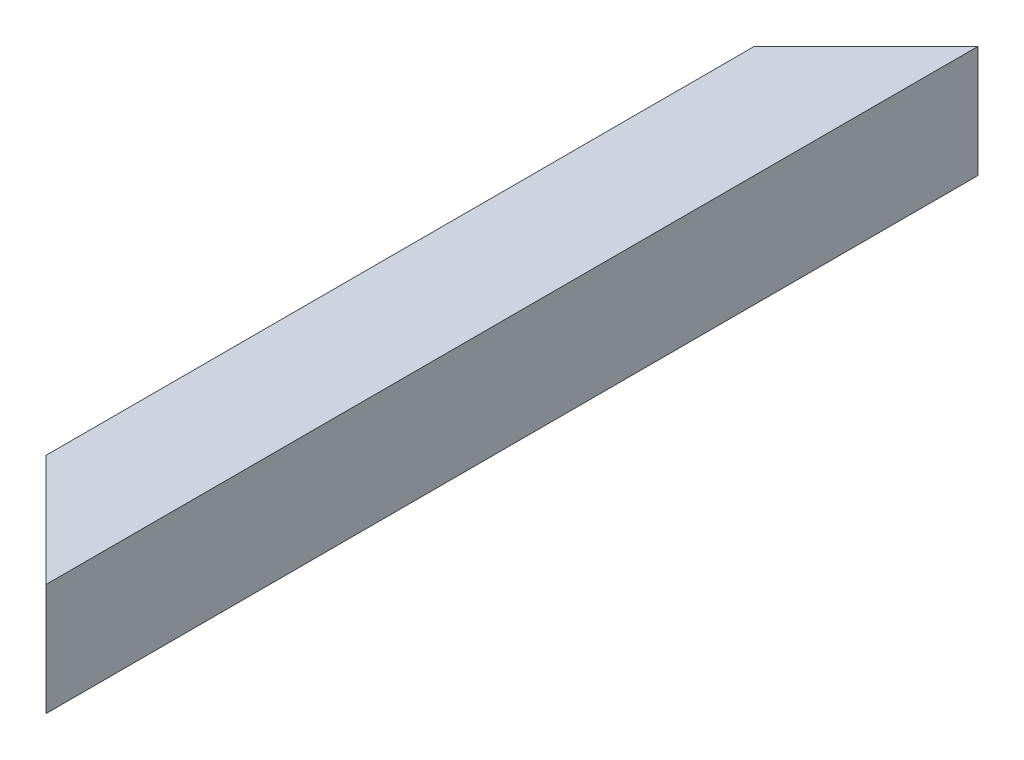
SolidWorks part; units mm, degrees
ref_plane "Front Plane" through (0, 0, 0) normal (0, 0, 1) x (1, 0, 0)
ref_plane "Top Plane" through (0, 0, 0) normal (0, 1, 0) x (1, 0, 0)
ref_plane "Right Plane" through (0, 0, 0) normal (1, 0, 0) x (0, 0, -1)
curve "Curve1"
  spline degree 1 poles (0, 0, 0) (0, 0, 500) knots 0 0 1 1
sketch "Sketch1" plane through (0, 0, 0) normal (0, 0, 1) x (1, 0, 0)
  line L0 (0, 35.3535) -> (0, -33.8384) construction
  line L1 (-30, 30) -> (30, 30)
  line L2 (-30, 30) -> (-30, -30)
  line L3 (-30, -30) -> (30, -30)
  line L4 (30, 30) -> (30, -30)
  line L5 (-26, 26) -> (26, 26)
  line L6 (-26, 26) -> (-26, -26)
  line L7 (-26, -26) -> (26, -26)
  line L8 (26, 26) -> (26, -26)
  line L9 (-39.3939, 0) -> (41.5152, 0) construction
  dimension "D1" = 60
  dimension "D2" = 52
sweep "Sweep1" add profiles "Sketch1" path "Curve1"
sketch "Sketch2" plane through (0, 30, 0) normal (0, 1, 0) x (1, 0, 0)
  line L0 (30, 0) -> (-30, -60)
  line L1 (-30, 0) -> (-30, -500) construction
  line L2 (-30, -60) -> (-30, 0)
  line L3 (-30, 0) -> (30, 0)
  line L4 (30, -500) -> (-30, -440)
  line L5 (-30, -440) -> (-30, -500)
  line L6 (-30, -500) -> (30, -500)
  dimension "D1" = 45
  dimension "D2" = 45
extrude "Cut-Extrude1" cut sketch "Sketch2" against normal through all
